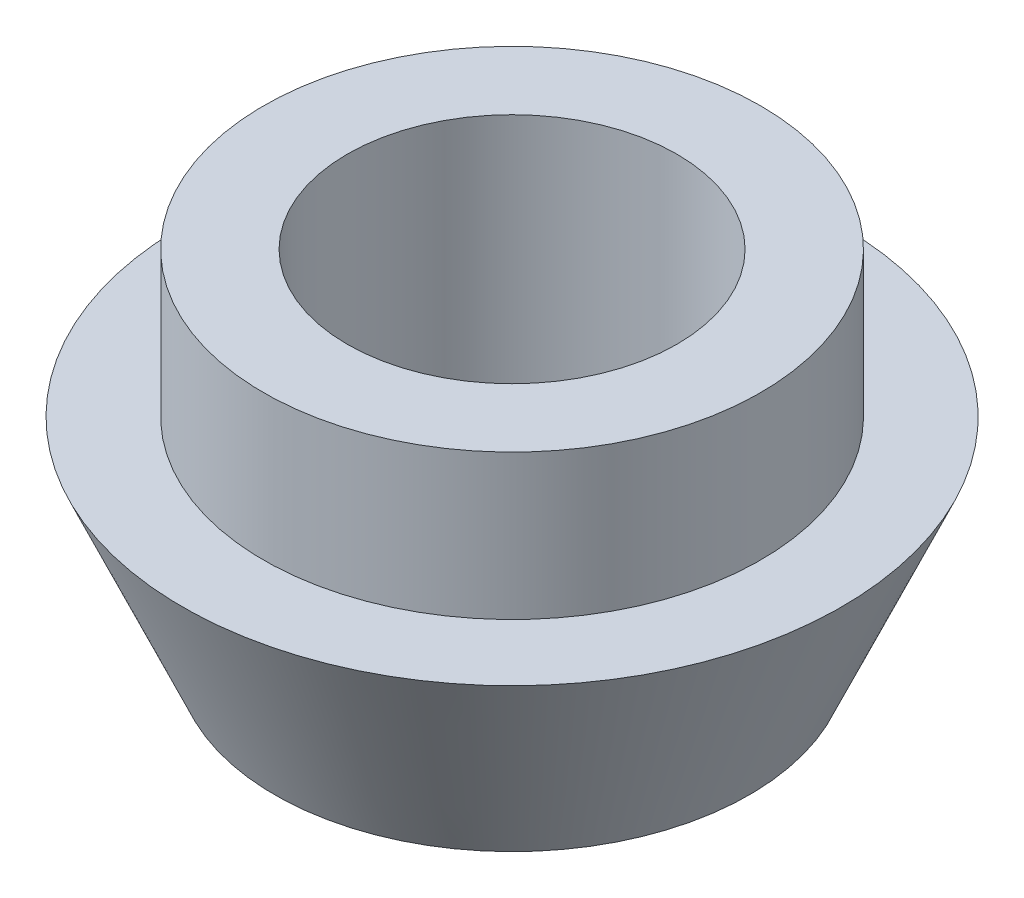
SolidWorks part; units mm, degrees
material "6061-T6 (SS)"
ref_plane "Front Plane" through (0, 0, 0) normal (0, 0, 1) x (1, 0, 0)
ref_plane "Top Plane" through (0, 0, 0) normal (0, 1, 0) x (1, 0, 0)
ref_plane "Right Plane" through (0, 0, 0) normal (1, 0, 0) x (0, 0, -1)
sketch "Sketch1" plane through (0, 0, 0) normal (0, 0, 1) x (1, 0, 0)
  line L0 (3.175, 0) -> (3.175, 6.8199)
  line L1 (3.175, 6.8199) -> (3.9688, 6.8199)
  line L2 (3.9688, 6.8199) -> (3.9688, 4.0259) construction
  line L3 (3.9688, 4.0259) -> (4.572, 4.0259) construction
  line L4 (4.572, 4.0259) -> (4.572, 0) construction
  line L5 (4.572, 0) -> (3.175, 0)
  line L6 (0, -15.0879) -> (0, 20.3358) construction
  line L7 (-4.572, 0) -> (-3.175, 0) construction
  line L8 (-4.572, 4.0259) -> (-4.572, 0) construction
  line L9 (-3.9688, 4.0259) -> (-4.572, 4.0259) construction
  line L10 (-3.9688, 6.8199) -> (-3.9688, 4.0259) construction
  line L11 (-3.175, 6.8199) -> (-3.9688, 6.8199) construction
  line L12 (-3.175, 0) -> (-3.175, 6.8199) construction
  line L13 (4.572, 0) -> (6.35, 1.778) construction
  line L14 (6.35, 1.778) -> (6.35, 4.0259) construction
  line L15 (3.9688, 6.8199) -> (4.7879, 6.8199)
  line L16 (4.7879, 6.8199) -> (4.7879, 4.0259)
  line L17 (4.7879, 4.0259) -> (6.35, 4.0259)
  line L18 (-4.572, 0) -> (-6.35, 1.778) construction
  line L19 (-4.7879, 4.0259) -> (-6.35, 4.0259) construction
  line L20 (-6.35, 1.778) -> (-6.35, 4.0259) construction
  line L21 (-4.7879, 6.8199) -> (-4.7879, 4.0259) construction
  line L22 (-3.9688, 6.8199) -> (-4.7879, 6.8199) construction
  line L23 (4.572, 0) -> (6.35, 4.0259)
  dimension "D1" = 6.35
  dimension "D2" = 4.0259
  dimension "D3" = 0.7938
  dimension "D4" = 2.794
  dimension "D5" = 9.144
  dimension "D6" = 45
  dimension "D7" = 9.5758
  dimension "D8" = 6.35
revolve "Revolve1" add sketch "Sketch1" angle 360 about L6
